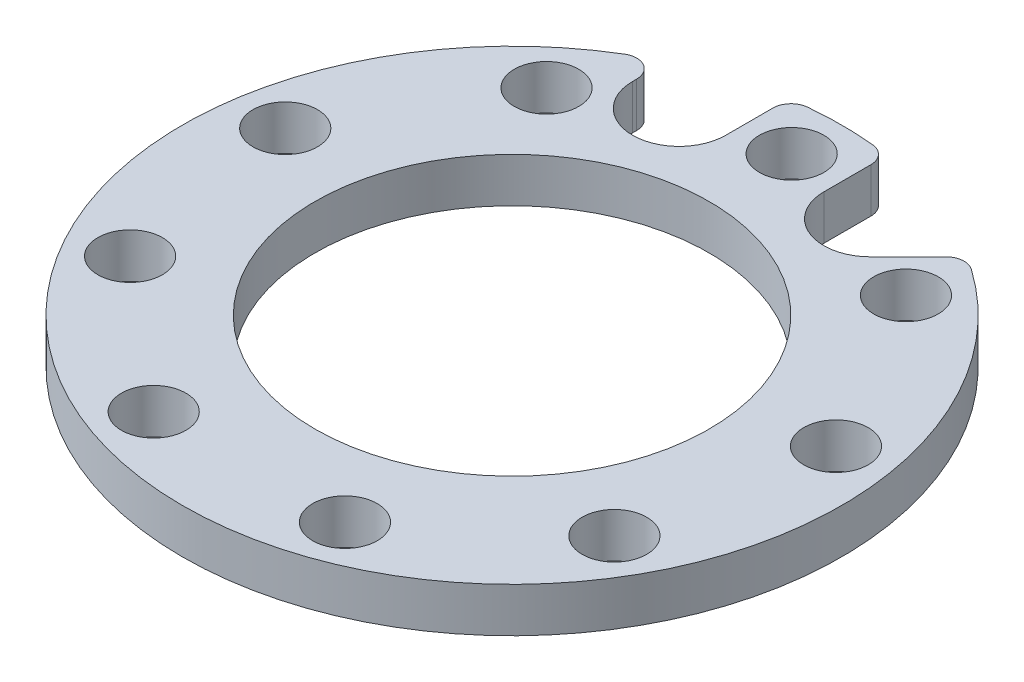
SolidWorks part; units mm, degrees
material "6061-T6 (SS)"
ref_plane "X-Y Datum" through (0, 0, 0) normal (0, 0, 1) x (1, 0, 0)
ref_plane "X-Z Datum" through (0, 0, 0) normal (0, 1, 0) x (1, 0, 0)
ref_plane "Y-Z Datum" through (0, 0, 0) normal (1, 0, 0) x (0, 0, -1)
sketch "Sketch1" plane through (0, 0, 0) normal (0, 1, 0) x (1, 0, 0)
  circle A0 centre (0, 0) radius 45.974
  circle A1 centre (0, 0) radius 39 construction
  circle A2 centre (0, 0) radius 25.908 construction
  circle A3 centre (0, 0) radius 27.4955
  circle A6 centre (-13.3388, 36.648) radius 6.5
  circle A7 centre (13.3388, 36.648) radius 6.5
  point P7 (0, 39)
  point P11 (13.3388, 36.648)
  point P12 (25.0687, 29.8757)
  point P13 (33.775, 19.5)
  point P14 (38.4075, 6.7723)
  point P15 (38.4075, -6.7723)
  point P16 (33.775, -19.5)
  point P17 (25.0687, -29.8757)
  point P18 (13.3388, -36.648)
  point P19 (0, -39)
  point P20 (-13.3388, -36.648)
  point P21 (-25.0687, -29.8757)
  point P22 (-33.775, -19.5)
  point P23 (-38.4075, -6.7723)
  point P24 (-38.4075, 6.7723)
  point P25 (-33.775, 19.5)
  point P26 (-25.0687, 29.8757)
  point P27 (-13.3388, 36.648)
  point P28 (0, 0)
  dimension "D1" = 91.948
  dimension "D2" = 78
  dimension "D3" = 51.816
  dimension "D6" = 13
  dimension "D4" = 1.5875
  dimension "D5" = 18
extrude "Boss-Extrude1" add sketch "Sketch1" along normal blind 6.214
hole_wizard "M8 Clearance Hole1" positions "Sketch4" profile "Sketch5" hole size "M8" standard "ANSI Metric" end condition through all
sketch "Sketch4" plane through (0, 6.214, 0) normal (0, 1, 0) x (1, 0, 0)
  point P0 (0, 39)
sketch "Sketch5" plane through (0, 6.214, -39) normal (1, 0, 0) x (0, 0, 1)
  line L0 (0, 0) -> (0, 6.214)
  line L1 (0, 6.214) -> (4.5, 6.214)
  line L2 (4.5, 6.214) -> (4.5, 0)
  line L5 (4.5, 0) -> (0, 0)
  line L11 (0, -6.35) -> (0, 107.95) construction
  dimension "Thru Hole Dia." = 9
  dimension "Thru Hole Depth" = 6.214
pattern_circular "CirPattern1" count 9 over 360 about axis through (0, 0, 0) along (0, 1, 0) of "M8 Clearance Hole1"
sketch "Sketch6" plane through (0, 6.214, 0) normal (0, 1, 0) x (1, 0, 0)
  line L0 (17.935, 32.0518) -> (24.6746, 38.7914)
  line L1 (6.8388, 36.648) -> (6.8388, 45.4625)
  line L2 (-6.8388, 36.648) -> (-6.8388, 45.4625)
  line L4 (-19.8388, 36.648) -> (-19.8388, 41.4733)
  circle A0 centre (-13.3388, 36.648) radius 6.5 construction
  circle A1 centre (13.3388, 36.648) radius 6.5 construction
  circle A2 centre (-13.3388, 36.648) radius 6.5 construction
  circle A3 centre (13.3388, 36.648) radius 6.5 construction
  circle A4 centre (0, 0) radius 45.974 construction
  arc A8 (6.8388, 45.4625) -> (24.6746, 38.7914) centre (0, 0) cw
  arc A10 (6.8388, 36.648) -> (17.935, 32.0518) centre (13.3388, 36.648) cw
  arc A11 (-19.8388, 36.648) -> (-6.8388, 36.648) centre (-13.3388, 36.648) cw
  arc A12 (-19.8388, 41.4733) -> (-6.8388, 45.4625) centre (0, 0) cw
  dimension "D2" = 6.7396
extrude "Cut-Extrude1" cut sketch "Sketch6" against normal through all
fillet "Fillet1" radius 2.54 4 edges at (24.6746, 3.107, -38.7914) (6.8388, 3.107, -45.4625) (-6.8388, 3.107, -45.4625) (-19.8388, 3.107, -41.4733)
